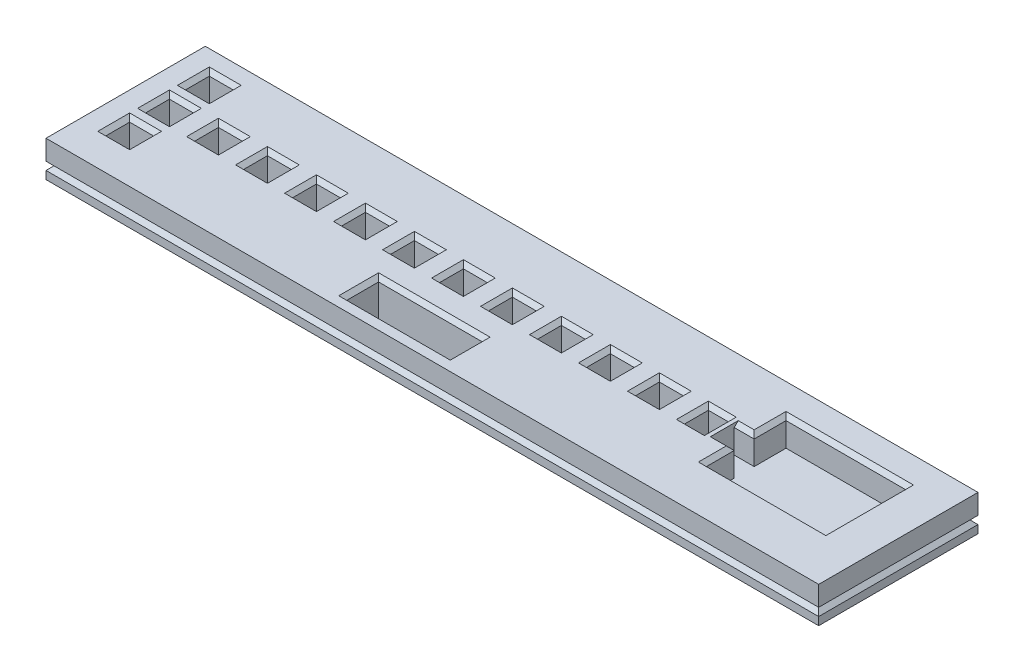
SolidWorks part; units mm, degrees
ref_plane "Front Plane" through (0, 0, 0) normal (0, 0, 1) x (1, 0, 0)
ref_plane "Top Plane" through (0, 0, 0) normal (0, 1, 0) x (1, 0, 0)
ref_plane "Right Plane" through (0, 0, 0) normal (1, 0, 0) x (0, 0, -1)
sketch "Sketch1" plane through (0, 0, 0) normal (0, 1, 0) x (1, 0, 0)
  line L1 (-97, -20) -> (97, -20)
  line L2 (-97, -20) -> (-97, 20)
  line L3 (-97, 20) -> (97, 20)
  line L4 (97, -20) -> (97, 20)
  line L5 (-97, -20) -> (97, 20) construction
  line L6 (-97, 20) -> (97, -20) construction
  point P0 (0, 0)
  dimension "D1" = 40
  dimension "D2" = 194
extrude "Boss-Extrude1" add sketch "Sketch1" along normal blind 10
sketch "Sketch3" plane through (0, 10, 0) normal (0, 1, 0) x (1, 0, 0)
  line L0 (0, 0) -> (50000, 0) construction
  line L1 (0, 0) -> (0, 50000) construction
  line L2 (0, 2) -> (50000, 2) construction
  line L6 (-91, 5) -> (-85, 5)
  line L7 (-91, 5) -> (-91, -1)
  line L8 (-91, -1) -> (-85, -1)
  line L9 (-85, 5) -> (-85, -1)
  line L10 (-91, 5) -> (-85, -1) construction
  line L11 (-91, -1) -> (-85, 5) construction
  line L12 (-78.7, 5) -> (-78.7, -1)
  line L13 (-78.7, 5) -> (-72.7, 5)
  line L14 (-72.7, 5) -> (-72.7, -1)
  line L15 (-78.7, -1) -> (-72.7, -1)
  line L16 (-66.4, 5) -> (-66.4, -1)
  line L17 (-66.4, 5) -> (-60.4, 5)
  line L18 (-60.4, 5) -> (-60.4, -1)
  line L19 (-66.4, -1) -> (-60.4, -1)
  line L20 (-54.1, 5) -> (-54.1, -1)
  line L21 (-54.1, 5) -> (-48.1, 5)
  line L22 (-48.1, 5) -> (-48.1, -1)
  line L23 (-54.1, -1) -> (-48.1, -1)
  line L24 (-41.8, 5) -> (-41.8, -1)
  line L25 (-41.8, 5) -> (-35.8, 5)
  line L26 (-35.8, 5) -> (-35.8, -1)
  line L27 (-41.8, -1) -> (-35.8, -1)
  line L28 (-29.5, 5) -> (-29.5, -1)
  line L29 (-29.5, 5) -> (-23.5, 5)
  line L30 (-23.5, 5) -> (-23.5, -1)
  line L31 (-29.5, -1) -> (-23.5, -1)
  line L32 (-17.2, 5) -> (-17.2, -1)
  line L33 (-17.2, 5) -> (-11.2, 5)
  line L34 (-11.2, 5) -> (-11.2, -1)
  line L35 (-17.2, -1) -> (-11.2, -1)
  line L36 (-4.9, 5) -> (-4.9, -1)
  line L37 (-4.9, 5) -> (1.1, 5)
  line L38 (1.1, 5) -> (1.1, -1)
  line L39 (-4.9, -1) -> (1.1, -1)
  line L40 (7.4, 5) -> (7.4, -1)
  line L41 (7.4, 5) -> (13.4, 5)
  line L42 (13.4, 5) -> (13.4, -1)
  line L43 (7.4, -1) -> (13.4, -1)
  line L44 (19.7, 5) -> (19.7, -1)
  line L45 (19.7, 5) -> (25.7, 5)
  line L46 (25.7, 5) -> (25.7, -1)
  line L47 (19.7, -1) -> (25.7, -1)
  line L48 (32, 5) -> (32, -1)
  line L49 (32, 5) -> (38, 5)
  line L50 (38, 5) -> (38, -1)
  line L51 (32, -1) -> (38, -1)
  line L52 (44.3, 5) -> (44.3, -1)
  line L53 (44.3, 5) -> (50.3, 5)
  line L54 (50.3, 5) -> (50.3, -1)
  line L55 (44.3, -1) -> (50.3, -1)
  line L56 (-91, 15) -> (-91, 9)
  line L57 (-91, 15) -> (-85, 15)
  line L58 (-85, 15) -> (-85, 9)
  line L59 (-91, 9) -> (-85, 9)
  line L60 (-91, -5) -> (-91, -11)
  line L61 (-91, -5) -> (-85, -5)
  line L62 (-85, -5) -> (-85, -11)
  line L63 (-91, -11) -> (-85, -11)
  line L65 (-25, -8.5) -> (1, -8.5)
  line L66 (-25, -8.5) -> (-25, -16.5)
  line L67 (-25, -16.5) -> (1, -16.5)
  line L68 (1, -8.5) -> (1, -16.5)
  line L69 (-25, -8.5) -> (1, -16.5) construction
  line L70 (-25, -16.5) -> (1, -8.5) construction
  line L73 (-97, 20) -> (-97, -20) construction
  line L74 (-97, 20) -> (-97, -20) construction
  line L75 (97, 20) -> (-97, 20) construction
  line L76 (-97, -20) -> (97, -20) construction
  point P11 (-88, 2)
  point P69 (-12, -12.5)
  dimension "D2" = 6
  dimension "D3" = 6
  dimension "D4" = 6
  dimension "D6" = 2
  dimension "D8" = 8
  dimension "D9" = 26
  dimension "D10" = 3.5
  dimension "D11" = 72
  dimension "D12" = 18
  dimension "D13" = 6.3
  dimension "D5" = 12
  dimension "D7" = 2
extrude "Cut-Extrude1" cut sketch "Sketch3" against normal through all
chamfer "Chamfer1" distance 1 angle 45 59 edges at (44.3, 10, -2) (47.3, 10, 1) (47.3, 10, -5) (32, 10, -2) (35, 10, 1) (38, 10, -2) (35, 10, -5) (19.7, 10, -2) (22.7, 10, 1) (25.7, 10, -2) (22.7, 10, -5) (7.4, 10, -2) (10.4, 10, 1) (13.4, 10, -2) (10.4, 10, -5) (-4.9, 10, -2) (-1.9, 10, 1) (1.1, 10, -2) (-1.9, 10, -5) (-17.2, 10, -2) (-14.2, 10, 1) (-11.2, 10, -2) (-14.2, 10, -5) (-29.5, 10, -2) (-26.5, 10, 1) (-23.5, 10, -2) (-26.5, 10, -5) (-35.8, 10, -2) (-38.8, 10, 1) (-41.8, 10, -2) (-38.8, 10, -5) (-54.1, 10, -2) (-51.1, 10, 1) (-48.1, 10, -2) (-51.1, 10, -5) (-66.4, 10, -2) (-63.4, 10, 1) (-60.4, 10, -2) (-63.4, 10, -5) (-75.7, 10, 1) (-72.7, 10, -2) (-75.7, 10, -5) (-78.7, 10, -2) (-88, 10, 11) (-85, 10, 8) (-91, 10, 8) (-88, 10, 5) (-85, 10, -2) (-88, 10, 1) (-91, 10, -2) (-88, 10, -5) (-85, 10, -12) (-88, 10, -9) (-91, 10, -12) (-88, 10, -15) (1, 10, 12.5) (-12, 10, 16.5) (-25, 10, 12.5) (-12, 10, 8.5)
chamfer "Chamfer2" distance 1 angle 45 64 edges at (0, 0, -20) (-97, 0, 0) (0, 0, 20) (97, 0, 0) (-88, 0, 1) (-91, 0, -2) (-88, 0, -5) (-85, 0, -2) (-12, 0, 16.5) (-25, 0, 12.5) (-12, 0, 8.5) (1, 0, 12.5) (-91, 0, -12) (-88, 0, -15) (-85, 0, -12) (-88, 0, -9) (19.7, 0, -2) (22.7, 0, -5) (25.7, 0, -2) (22.7, 0, 1) (32, 0, -2) (35, 0, -5) (38, 0, -2) (35, 0, 1) (44.3, 0, -2) (47.3, 0, -5) (50.3, 0, -2) (47.3, 0, 1) (-91, 0, 8) (-88, 0, 5) (-85, 0, 8) (-88, 0, 11) (7.4, 0, -2) (10.4, 0, -5) (13.4, 0, -2) (10.4, 0, 1) (-4.9, 0, -2) (-1.9, 0, -5) (1.1, 0, -2) (-1.9, 0, 1) (-17.2, 0, -2) (-14.2, 0, -5) (-11.2, 0, -2) (-14.2, 0, 1) (-29.5, 0, -2) (-26.5, 0, -5) (-23.5, 0, -2) (-26.5, 0, 1) (-41.8, 0, -2) (-38.8, 0, -5) (-35.8, 0, -2) (-38.8, 0, 1) (-54.1, 0, -2) (-51.1, 0, -5) (-48.1, 0, -2) (-51.1, 0, 1) (-66.4, 0, -2) (-63.4, 0, -5) (-60.4, 0, -2) (-63.4, 0, 1) (-78.7, 0, -2) (-75.7, 0, -5) (-72.7, 0, -2) (-75.7, 0, 1)
sketch "Sketch4" plane through (0, 10, 0) normal (0, 1, 0) x (1, 0, 0)
  line L1 (51.3, 4.5) -> (56.3, 4.5)
  line L2 (51.3, 4.5) -> (51.3, -0.5)
  line L3 (51.3, -0.5) -> (56.3, -0.5)
  line L4 (56.3, 4.5) -> (56.3, -0.5)
  line L5 (51.3, 4.5) -> (56.3, -0.5) construction
  line L6 (51.3, -0.5) -> (56.3, 4.5) construction
  line L7 (44.3, -1) -> (50.3, -1) construction
  line L9 (56.3, 12.5) -> (86.3, 12.5)
  line L10 (56.3, 12.5) -> (56.3, -7.5)
  line L11 (56.3, -7.5) -> (86.3, -7.5)
  line L12 (86.3, 12.5) -> (86.3, -7.5)
  line L13 (56.3, 12.5) -> (86.3, -7.5) construction
  line L14 (56.3, -7.5) -> (86.3, 12.5) construction
  line L15 (50.3, -2) -> (50.3, 6) construction
  line L16 (97, 20) -> (-97, 20) construction
  point P0 (53.8, 2)
  point P9 (71.3, 2.5)
  dimension "D1" = 1
  dimension "D2" = 5
  dimension "D3" = 5
  dimension "D4" = 0.5
  dimension "D5" = 30
  dimension "D6" = 20
  dimension "D7" = 7.5
  dimension "D8" = 0
extrude "Cut-Extrude2" cut sketch "Sketch4" against normal blind 7 contours L4 L1 L2 L3 | L12 L9 L10 L4 L11
chamfer "Chamfer3" distance 1 angle 45 7 edges at (53.8, 10, 0.5) (53.8, 10, -4.5) (56.3, 10, -8.5) (86.3, 10, -2.5) (71.3, 10, 7.5) (56.3, 10, 4) (71.3, 10, -12.5)
sketch "Sketch6" plane through (-97, 0, 0) normal (-1, 0, 0) x (0, 0, 1)
  line L0 (0, 0) -> (0, 50000) construction
  line L1 (-20, 5) -> (-20, 3)
  line L2 (-20, 10) -> (-20, 1) construction
  line L3 (-20, 3) -> (-19, 4)
  line L4 (-19, 4) -> (-20, 5)
  line L9 (19, 4) -> (20, 5)
  line L10 (20, 3) -> (19, 4)
  line L11 (20, 5) -> (20, 3)
  dimension "D1" = 45
  dimension "D2" = 45
  dimension "D3" = 2
  dimension "D4" = 2
sketch "Sketch7" plane through (0, 0, 20) normal (0, 0, 1) x (1, 0, 0)
  line L0 (-97, 5) -> (-96, 4)
  line L3 (-96, 4) -> (-97, 3)
  line L4 (-97, 3) -> (-97, 5)
  line L5 (-97, 1) -> (97, 1) construction
  line L6 (0, 0) -> (0, 50000) construction
  line L7 (96, 4) -> (97, 3)
  line L8 (97, 5) -> (96, 4)
  line L9 (97, 3) -> (97, 5)
  line L10 (-97, 10) -> (-97, 1) construction
  dimension "D1" = 45
  dimension "D2" = 45
  dimension "D3" = 2
  dimension "D4" = 2
extrude "Cut-Extrude4" cut sketch "Sketch6" against normal through all
extrude "Cut-Extrude5" cut sketch "Sketch7" against normal through all
